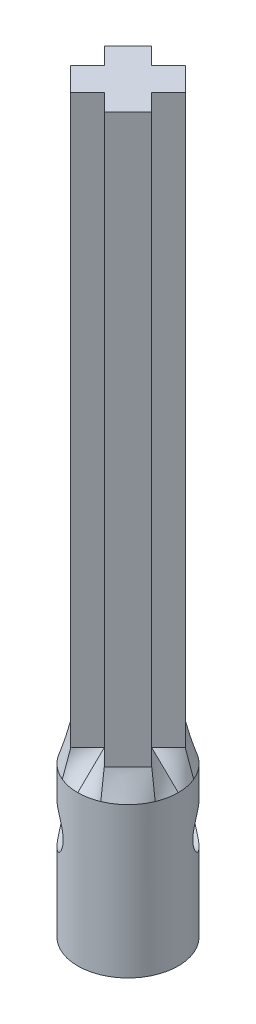
SolidWorks part; units mm, degrees
ref_plane "Front Plane" through (0, 0, 0) normal (0, 0, 1) x (1, 0, 0)
ref_plane "Top Plane" through (0, 0, 0) normal (0, 1, 0) x (1, 0, 0)
ref_plane "Right Plane" through (0, 0, 0) normal (1, 0, 0) x (0, 0, -1)
sketch "Sketch1" plane through (0, 0, 0) normal (0, 1, 0) x (1, 0, 0)
  line L0 (-0.627, 2.9162) -> (-2.423, 4.7122)
  line L1 (-3.167, -2.1638) -> (1.913, -2.1638) construction
  line L2 (-3.167, -2.1638) -> (-3.167, 2.9162) construction
  line L3 (-3.167, 2.9162) -> (1.913, 2.9162) construction
  line L4 (1.913, -2.1638) -> (1.913, 2.9162) construction
  line L5 (-3.167, -2.1638) -> (1.913, 2.9162) construction
  line L6 (-3.167, 2.9162) -> (1.913, -2.1638) construction
  line L7 (-3.167, 0.3762) -> (-4.963, 2.1722)
  line L8 (-4.963, 2.1722) -> (-2.423, 4.7122)
  line L9 (1.913, 0.3762) -> (3.7091, -1.4199)
  line L10 (-0.627, -2.1638) -> (1.1691, -3.9599)
  line L11 (1.1691, -3.9599) -> (3.7091, -1.4199)
  line L12 (-3.167, 0.3762) -> (-4.963, -1.4199)
  line L13 (-0.627, -2.1638) -> (-2.423, -3.9599)
  line L14 (-4.963, -1.4199) -> (-2.423, -3.9599)
  line L15 (1.913, 0.3762) -> (3.7091, 2.1722)
  line L16 (1.1691, 4.7122) -> (3.7091, 2.1722)
  line L17 (-0.627, 2.9162) -> (1.1691, 4.7122)
  point P0 (-0.627, 0.3762)
  dimension "D1" = 2.54
  dimension "D2" = 5.08
  dimension "D3" = 5.08
  dimension "D4" = 8.6721
  dimension "D5" = 3.5921
  dimension "D6" = 3.5921
  dimension "D7" = 3.5921
  dimension "D8" = 3.5921
  dimension "D9" = 8.6721
  dimension "D10" = 0
  dimension "D11" = 3.5921
  dimension "D12" = 5.08
  dimension "D13" = 2.54
  dimension "D14" = 2.54
  dimension "D15" = 2.54
  dimension "D16" = 2.54
  dimension "D17" = 2.54
  dimension "D18" = 2.54
  dimension "D19" = 2.54
  dimension "D20" = 2.54
extrude "Boss-Extrude1" add sketch "Sketch1" along normal blind 60.7391
scale "Scale1" scale about centroid uniform scaling yes scale factor 0.92
ref_plane "Plane1" through (0, -0.1104, 0) normal (0, -1, 0) x (-1, 0, 0)
sketch "Sketch4" plane through (0, -0.1104, 0) normal (0, -1, 0) x (-1, 0, 0)
  line L0 (-1.7098, 0.3762) -> (2.9638, 0.3762) construction
  line L1 (0.627, 2.713) -> (0.627, -1.9606) construction
  circle A0 centre (0.627, 0.3762) radius 4.953
  dimension "D1" = 9.906
loft "Loft1" add profiles "Sketch4" section face at (-0.627, 2.4296, -0.3762) section "Sketch4"
sketch "Sketch3" plane through (0, -0.1104, 0) normal (0, 1, 0) x (1, 0, 0)
  line L0 (-2.9638, 0.3762) -> (1.7098, 0.3762) construction
  line L1 (-0.627, 2.713) -> (-0.627, -1.9606) construction
  circle A0 centre (-0.627, 0.3762) radius 4.953
  dimension "D1" = 9.906
extrude "Boss-Extrude2" add sketch "Sketch3" against normal blind 14.7955
ref_plane "Plane2" through (3.3769, 0, -3.3769) normal (0.7071, 0, -0.7071) x (-0.7071, 0, -0.7071)
sketch "Sketch5" plane through (3.3769, 0, -3.3769) normal (0.7071, 0, -0.7071) x (-0.7071, 0, -0.7071)
  line L0 (0.7093, -14.9059) -> (0.7093, -0.1104) construction
  line L1 (-4.2437, -14.9059) -> (5.6623, -14.9059) construction
  circle A0 centre (0.7093, -5.1904) radius 2.032
  dimension "D1" = 4.064
  dimension "D2" = 5.08
extrude "Cut-Extrude1" cut sketch "Sketch5" against normal through all
